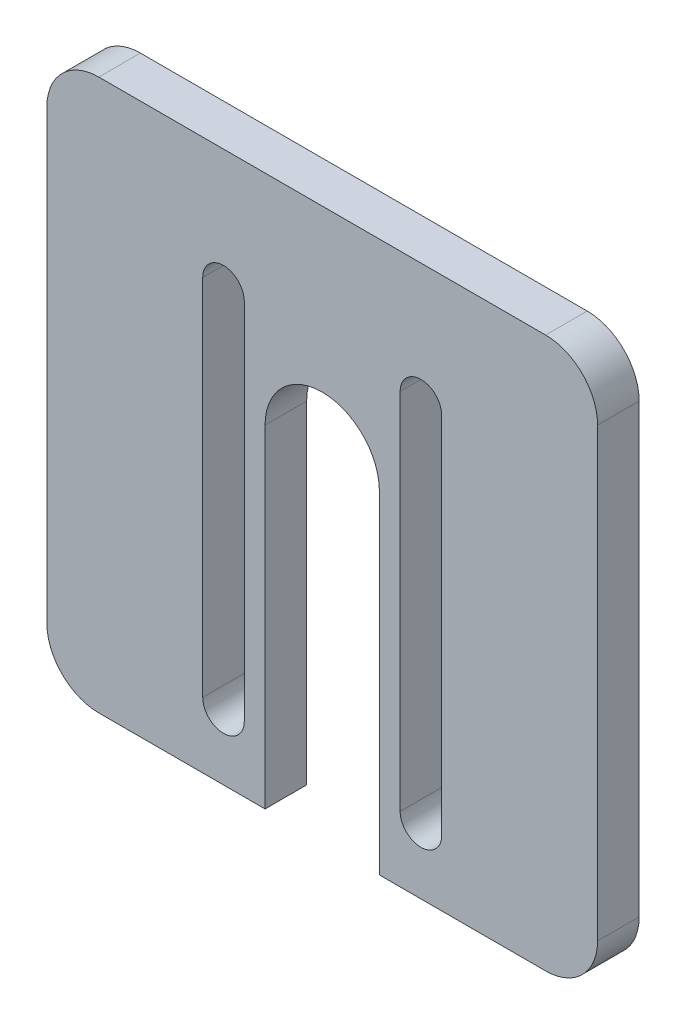
SolidWorks part; units mm, degrees
ref_plane "Front Plane" through (0, 0, 0) normal (0, 0, 1) x (1, 0, 0)
ref_plane "Top Plane" through (0, 0, 0) normal (0, 1, 0) x (1, 0, 0)
ref_plane "Right Plane" through (0, 0, 0) normal (1, 0, 0) x (0, 0, -1)
sketch "Sketch1" plane through (0, 0, 0) normal (0, 0, 1) x (1, 0, 0)
  line L0 (0, 5) -> (0, 48)
  line L1 (5, 53) -> (48, 53)
  line L2 (53, 48) -> (53, 5)
  line L3 (48, 0) -> (5, 0)
  line L4 (26.5, 0) -> (26.5, 53) construction
  line L5 (26.5, 31.995) -> (32, 31.995) construction
  line L6 (26.5, 31.995) -> (21, 31.995) construction
  line L7 (21, 31.995) -> (21, 0)
  line L8 (32, 31.995) -> (32, 0)
  line L9 (19, 6.3002) -> (19, 41.3002)
  line L10 (15, 6.3002) -> (15, 41.3002)
  line L11 (38, 6.3002) -> (38, 41.3002)
  line L12 (34, 6.3002) -> (34, 41.3002)
  arc A0 (21, 31.995) -> (32, 31.995) centre (26.5, 31.995) cw
  arc A1 (15, 41.3002) -> (19, 41.3002) centre (17, 41.3002) cw
  arc A2 (15, 6.3002) -> (19, 6.3002) centre (17, 6.3002) ccw
  arc A3 (38, 6.3002) -> (34, 6.3002) centre (36, 6.3002) cw
  arc A4 (38, 41.3002) -> (34, 41.3002) centre (36, 41.3002) ccw
  arc A5 (0, 5) -> (5, 0) centre (5, 5) ccw
  arc A6 (53, 5) -> (48, 0) centre (48, 5) cw
  arc A7 (48, 53) -> (53, 48) centre (48, 48) cw
  arc A8 (0, 48) -> (5, 53) centre (5, 48) cw
  point P27 (0, 0)
  point P30 (53, 0)
  point P35 (0, 53)
  dimension "D7" = 5
  dimension "D1" = 53
  dimension "D2" = 53
  dimension "D3" = 5.5
  dimension "D4" = 2
  dimension "D5" = 4
  dimension "D6" = 35
extrude "Boss-Extrude2" add sketch "Sketch1" along normal blind 4 contours A8 L0 A5 L3 L7 A0 L8 A6 L2 A7 L1 A4 L11 A3 L12 A2 L10 A1 L9
